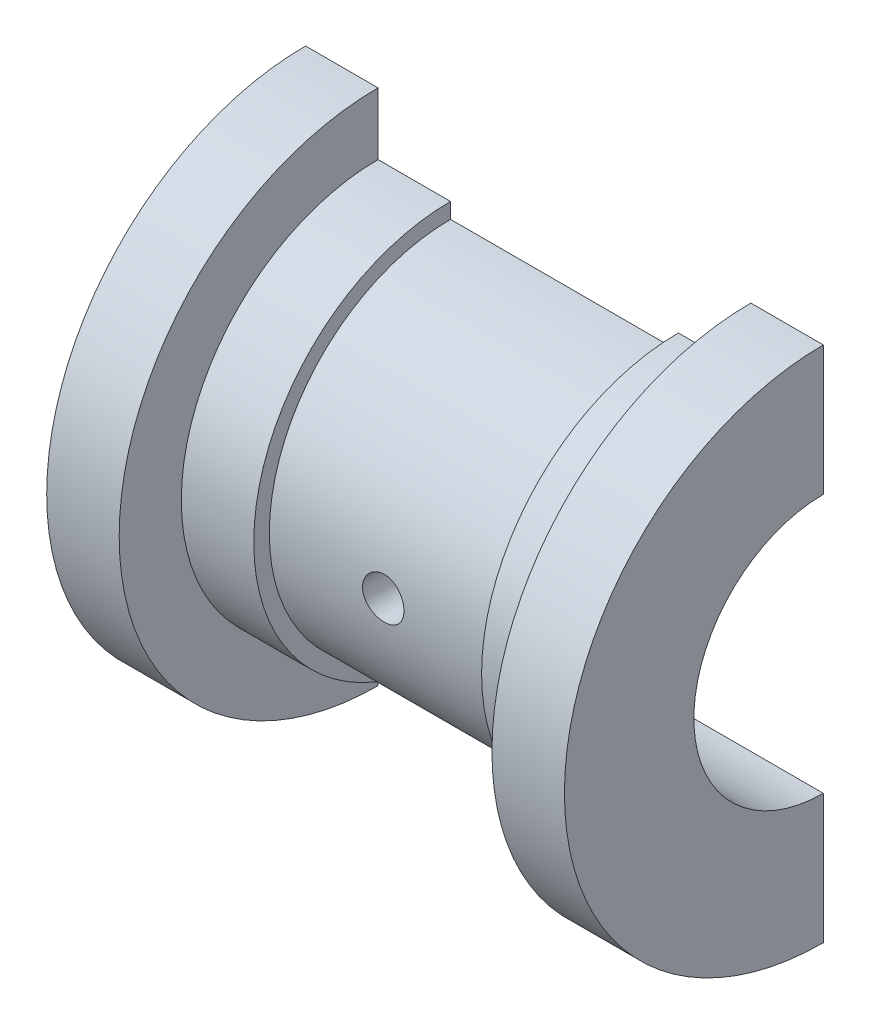
SolidWorks part; units mm, degrees
ref_plane "Front Plane" through (0, 0, 0) normal (0, 0, 1) x (1, 0, 0)
ref_plane "Top Plane" through (0, 0, 0) normal (0, 1, 0) x (1, 0, 0)
ref_plane "Right Plane" through (0, 0, 0) normal (1, 0, 0) x (0, 0, -1)
sketch "Sketch1" plane through (0, 0, 0) normal (0, 0, 1) x (1, 0, 0)
  line L0 (-38.9494, 0) -> (38.9494, 0) construction
  line L1 (0, 19.9347) -> (0, 17.5) construction
  line L2 (25, 0) -> (-25, 0)
  line L3 (-25, 0) -> (-25, 25)
  line L4 (-25, 25) -> (-18, 25)
  line L5 (-18, 25) -> (-18, 19)
  line L6 (-18, 19) -> (-11, 19)
  line L7 (-11, 19) -> (-11, 17.5)
  line L8 (-11, 17.5) -> (11, 17.5)
  line L10 (11, 19) -> (11, 17.5)
  line L11 (18, 19) -> (11, 19)
  line L12 (18, 25) -> (18, 19)
  line L13 (25, 25) -> (18, 25)
  line L14 (25, 0) -> (25, 25)
  line L15 (0, 0) -> (0, -19.9347) construction
  point P3 (0, 0)
  dimension "D1" = 25
  dimension "D2" = 25
  dimension "D5" = 19
  dimension "D6" = 17.5
revolve "Revolve1" add sketch "Sketch1" angle 180 about L0
sketch "Sketch2" plane through (-25, 0, 0) normal (-1, 0, 0) x (0, 0, 1)
  line L0 (0, -25) -> (0, 25) construction
  line L1 (0, 12.5) -> (0, -12.5)
  arc A0 (0, -12.5) -> (0, 12.5) centre (0, 0) ccw
extrude "Cut-Extrude3" cut sketch "Sketch2" against normal blind 50
ref_plane "Plane2" through (0, 0, 17.5) normal (0, 0, -1) x (-1, 0, 0)
sketch "Sketch4" plane through (0, 0, 17.5) normal (0, 0, -1) x (-1, 0, 0)
  circle A0 centre (0, 0) radius 2
  dimension "D1" = 4
extrude "Cut-Extrude4" cut sketch "Sketch4" along normal blind 43
